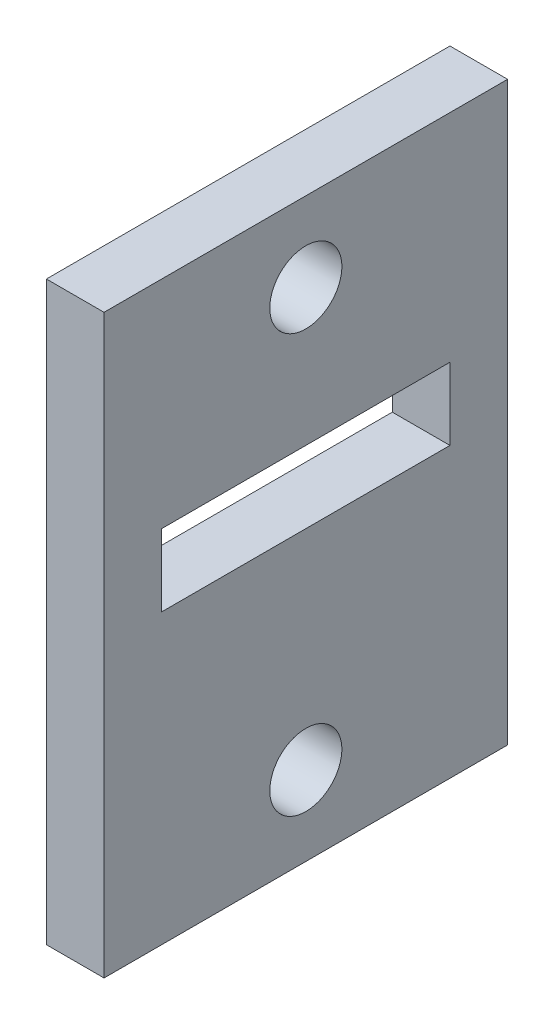
SolidWorks part; units mm, degrees
ref_plane "Front Plane" through (0, 0, 0) normal (0, 0, 1) x (1, 0, 0)
ref_plane "Top Plane" through (0, 0, 0) normal (0, 1, 0) x (1, 0, 0)
ref_plane "Right Plane" through (0, 0, 0) normal (1, 0, 0) x (0, 0, -1)
sketch "Sketch1" plane through (-64.0578, 0, 0) normal (-1, 0, 0) x (0, 0, 1)
  line L1 (18, 6.3986) -> (32, 6.3986)
  line L2 (18, 6.3986) -> (18, -13.6014)
  line L3 (18, -13.6014) -> (32, -13.6014)
  line L4 (32, 6.3986) -> (32, -13.6014)
  line L5 (18, 6.3986) -> (32, -13.6014) construction
  line L6 (18, -13.6014) -> (32, 6.3986) construction
  circle A0 centre (25, -10.8514) radius 1.25 construction
  circle A1 centre (25, 3.6486) radius 1.25 construction
  circle A2 centre (25, -10.8514) radius 1.25
  circle A3 centre (25, 3.6486) radius 1.25
  point P4 (25, -3.6014)
extrude "Boss-Extrude1" add sketch "Sketch1" along normal blind 2
sketch "Sketch2" plane through (-66.0578, 0, 0) normal (-1, 0, 0) x (0, 0, 1)
  line L0 (18, 6.3986) -> (18, -13.6014) construction
  line L1 (20, -1.1014) -> (30, -1.1014)
  line L2 (20, -1.1014) -> (20, -3.6014)
  line L3 (20, -3.6014) -> (30, -3.6014)
  line L4 (30, -1.1014) -> (30, -3.6014)
  line L5 (20, -1.1014) -> (30, -3.6014) construction
  line L6 (20, -3.6014) -> (30, -1.1014) construction
  line L7 (32, -13.6014) -> (32, 6.3986) construction
  line L8 (18, -13.6014) -> (32, -13.6014) construction
  line L9 (32, 6.3986) -> (18, 6.3986) construction
  point P4 (25, -2.3514)
  dimension "D1" = 2
  dimension "D2" = 2
  dimension "D3" = 10
  dimension "D4" = 7.5
extrude "Cut-Extrude1" cut sketch "Sketch2" against normal blind 2
equation "\"D1@Sketch2\"=\"D2@Sketch2\""
